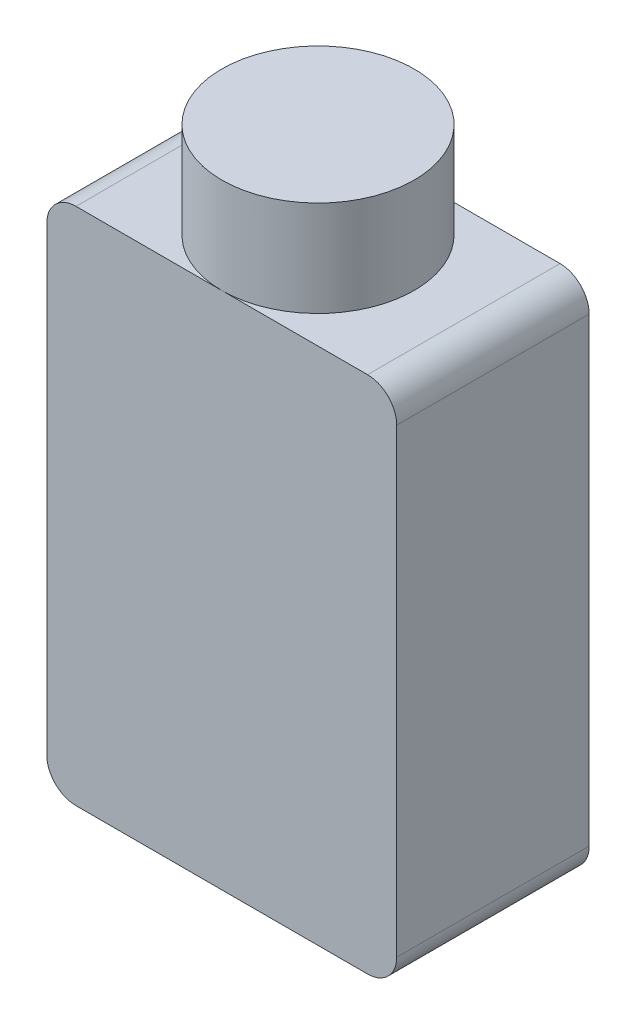
SolidWorks part; units mm, degrees
ref_plane "Front Plane" through (0, 0, 0) normal (0, 0, 1) x (1, 0, 0)
ref_plane "Top Plane" through (0, 0, 0) normal (0, 1, 0) x (1, 0, 0)
ref_plane "Right Plane" through (0, 0, 0) normal (1, 0, 0) x (0, 0, -1)
sketch "Sketch1" plane through (0, 0, 0) normal (0, 1, 0) x (1, 0, 0)
  line L1 (-19.05, -10.4775) -> (19.05, -10.4775)
  line L2 (-19.05, -10.4775) -> (-19.05, 10.4775)
  line L3 (-19.05, 10.4775) -> (19.05, 10.4775)
  line L4 (19.05, -10.4775) -> (19.05, 10.4775)
  line L5 (-19.05, -10.4775) -> (19.05, 10.4775) construction
  line L6 (-19.05, 10.4775) -> (19.05, -10.4775) construction
  point P0 (0, 0)
  dimension "D1" = 38.1
  dimension "D2" = 20.955
extrude "Boss-Extrude1" add sketch "Sketch1" along normal blind 56.515
fillet "Fillet1" radius 3.175 4 edges at (-19.05, 56.515, 0) (-19.05, 0, 0) (19.05, 0, 0) (19.05, 56.515, 0)
sketch "Sketch2" plane through (0, 56.515, 0) normal (0, 1, 0) x (1, 0, 0)
  circle A0 centre (0, 0) radius 10.4775
  dimension "D1" = 20.955
extrude "Boss-Extrude2" add sketch "Sketch2" along normal blind 10.414
